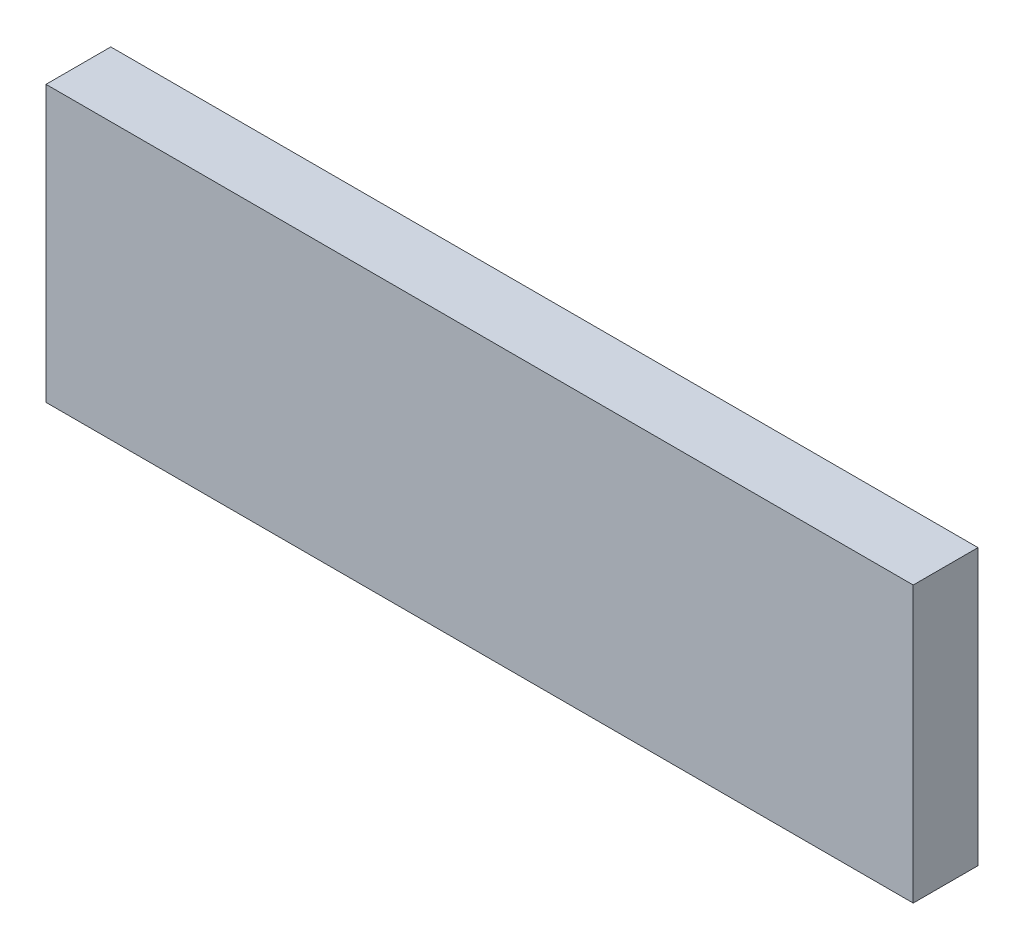
SolidWorks part; units mm, degrees
ref_plane "Front Plane" through (0, 0, 0) normal (0, 0, 1) x (1, 0, 0)
ref_plane "Top Plane" through (0, 0, 0) normal (0, 1, 0) x (1, 0, 0)
ref_plane "Right Plane" through (0, 0, 0) normal (1, 0, 0) x (0, 0, -1)
sketch "Sketch1" plane through (0, 0, 0) normal (0, 0, 1) x (1, 0, 0)
  line L1 (0, 0) -> (340, 0)
  line L2 (0, 0) -> (0, 108)
  line L3 (0, 108) -> (340, 108)
  line L4 (340, 0) -> (340, 108)
extrude "Boss-Extrude1" add sketch "Sketch1" along normal blind 25.4
